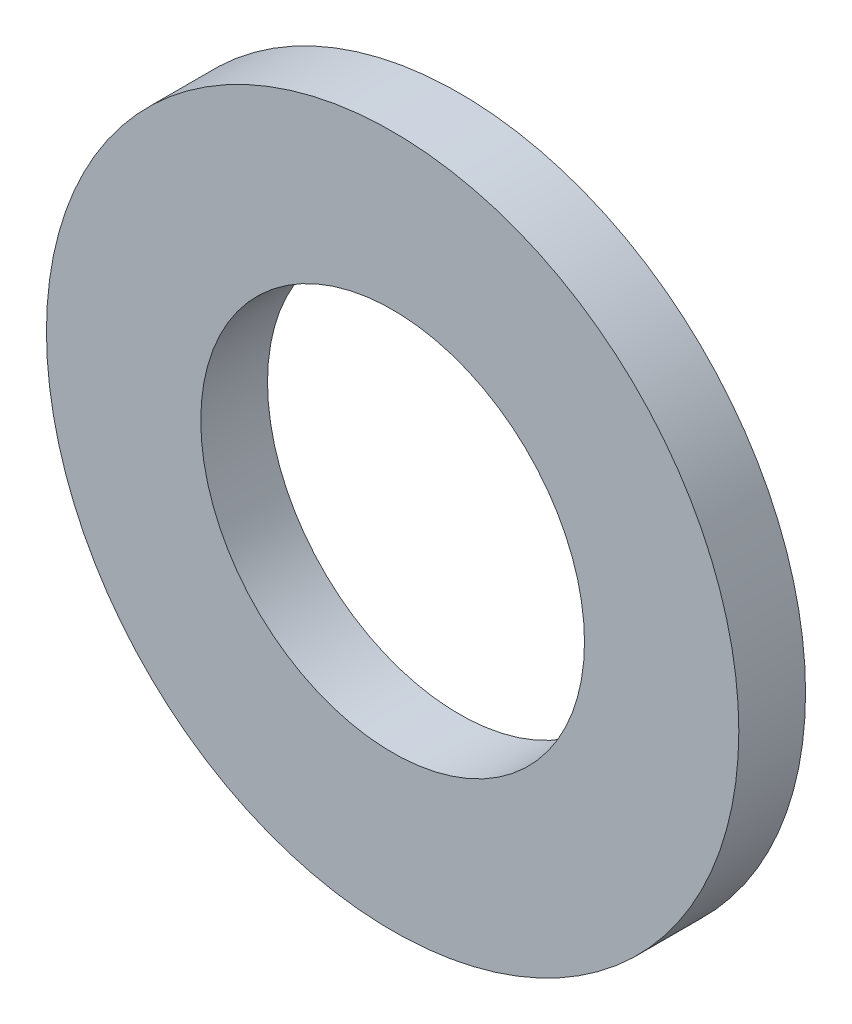
SolidWorks part; units mm, degrees
ref_plane "Front Plane" through (0, 0, 0) normal (0, 0, 1) x (1, 0, 0)
ref_plane "Top Plane" through (0, 0, 0) normal (0, 1, 0) x (1, 0, 0)
ref_plane "Right Plane" through (0, 0, 0) normal (1, 0, 0) x (0, 0, -1)
sketch "Sketch1" plane through (0, 0, 0) normal (0, 0, 1) x (1, 0, 0)
  circle A0 centre (0, 0) radius 4.6
  circle A1 centre (0, 0) radius 8.3
  dimension "D1" = 9.2
  dimension "D2" = 16.6
extrude "Boss-Extrude1" add sketch "Sketch1" along normal blind 1.6 contours A1 | A0
